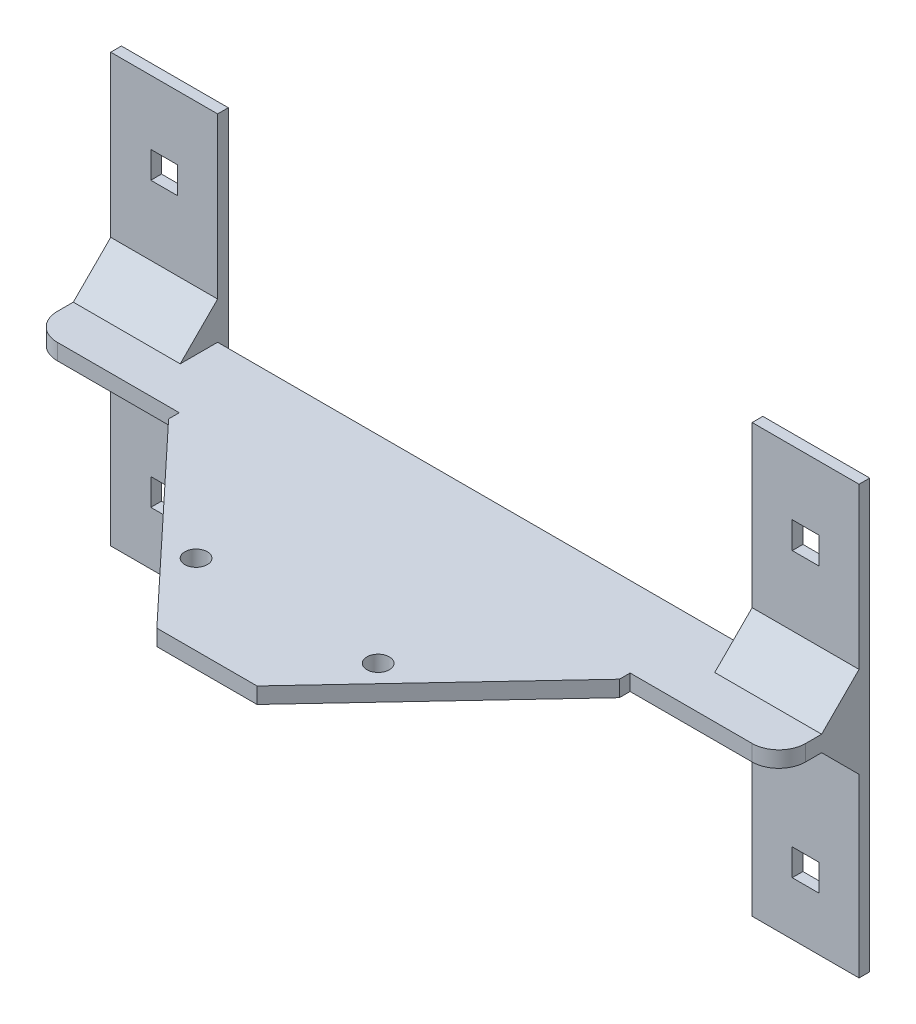
SolidWorks part; units mm, degrees
ref_plane "Front Plane" through (0, 0, 0) normal (0, 0, 1) x (1, 0, 0)
ref_plane "Top Plane" through (0, 0, 0) normal (0, 1, 0) x (1, 0, 0)
ref_plane "Right Plane" through (0, 0, 0) normal (1, 0, 0) x (0, 0, -1)
sketch "Sketch1" plane through (0, 0, 0) normal (0, 1, 0) x (1, 0, 0)
  line L0 (39.4127, 0.6403) -> (-2.757, 45.6403)
  line L2 (-2.757, 45.6403) -> (39.4127, 45.6403)
  line L3 (39.4127, 45.6403) -> (39.4127, 0.6403)
  line L4 (-2.757, 45.6403) -> (-2.757, 47.6403)
  line L5 (-2.757, 47.6403) -> (39.4127, 47.6403)
  line L6 (39.4127, 47.6403) -> (39.4127, 45.6403)
  circle A0 centre (22.3813, 25.641) radius 2.1
  dimension "D1" = 2
sketch "Sketch4" plane through (0, 0, 0) normal (0, 1, 0) x (1, 0, 0)
  line L0 (-2.757, 47.6403) -> (81.5825, 47.6403)
  line L1 (39.4127, 47.6403) -> (39.4127, 0.6403)
  line L2 (39.4127, 0.6403) -> (-2.757, 45.6403)
  line L3 (-2.757, 45.6403) -> (-2.757, 47.6403)
  line L4 (39.4127, 0.6403) -> (81.5825, 45.6403)
  line L5 (81.5825, 45.6403) -> (81.5825, 47.6403)
  circle A0 centre (22.3813, 25.641) radius 2.1
  circle A1 centre (56.4442, 25.641) radius 2.1
extrude "Boss-Extrude3" add sketch "Sketch4" along normal blind 1.2 contours L3 L2 L1 L0 A0 | L4 L5 L0 L1 A1
sketch "Sketch5" plane through (0, 0, 0) normal (0, -1, 0) x (-1, 0, 0)
  line L1 (2.757, 45.6403) -> (-81.5825, 45.6403)
  line L2 (2.757, 45.6403) -> (2.757, 47.6403)
  line L3 (2.757, 47.6403) -> (-81.5825, 47.6403)
  line L4 (-81.5825, 45.6403) -> (-81.5825, 47.6403)
extrude "Boss-Extrude4" add sketch "Sketch5" along normal blind 2.4
sketch "Sketch6" plane through (0, -2.4, 0) normal (0, -1, 0) x (-1, 0, 0)
  line L0 (2.757, 47.6403) -> (-81.5825, 47.6403)
  line L1 (-81.5825, 47.6403) -> (-81.5825, 45.6403)
  line L2 (-81.5825, 45.6403) -> (-39.4127, 0.6403)
  line L3 (-39.4127, 0.6403) -> (2.757, 45.6403)
  line L4 (2.757, 45.6403) -> (2.757, 47.6403)
  circle A0 centre (-22.3813, 25.641) radius 2.1
  circle A1 centre (-56.4442, 25.641) radius 2.1
extrude "Boss-Extrude5" add sketch "Sketch6" along normal blind 1.2
sketch "Sketch7" plane through (0, -3.6, 0) normal (0, -1, 0) x (-1, 0, 0)
  line L1 (15.2482, -5.1813) -> (-88.8196, -5.1813)
  line L2 (15.2482, -5.1813) -> (15.2482, 55.4712)
  line L3 (15.2482, 55.4712) -> (-88.8196, 55.4712)
  line L4 (-88.8196, -5.1813) -> (-88.8196, 55.4712)
extrude "Cut-Extrude1" cut sketch "Sketch7" against normal up to surface (3.6 mm away) contours L2 L1 L4 L3 up to face at (56.4442, 0, -23.541)
sketch "Sketch8" plane through (0, 1.2, 0) normal (0, 1, 0) x (1, 0, 0)
  line L0 (-2.757, 47.6403) -> (81.5825, 47.6403) construction
  line L1 (109.4127, 47.6403) -> (-30.5873, 47.6403)
  line L2 (39.4127, 47.6403) -> (39.4127, 62.6403)
  line L3 (109.4127, 62.6403) -> (-30.5873, 62.6403)
  line L4 (-30.5873, 47.6403) -> (-30.5873, 62.6403)
  line L5 (109.4127, 47.6403) -> (109.4127, 62.6403)
  line M11 (81.5825, 47.6403) -> (-2.757, 47.6403)
  dimension "D1" = 70
  dimension "D2" = 15
extrude "Boss-Extrude6" add sketch "Sketch8" against normal up to surface (1.2 mm away) contours L4 L1 L2 L3 | L1 L5 L3 L2 M11 up to face at (56.4442, 0, -23.541)
sketch "Sketch9" plane through (0, 1.2, 0) normal (0, 1, 0) x (1, 0, 0)
  line L0 (30.0417, 10.6403) -> (48.7838, 10.6403)
  line L1 (39.4127, 0.6403) -> (-2.757, 45.6403) construction
  line L2 (39.4127, 0.6403) -> (81.5825, 45.6403) construction
  line L3 (48.7838, 10.6403) -> (39.4127, 0.6403)
  line L4 (30.0417, 10.6403) -> (39.4127, 0.6403)
  dimension "D1" = 10
extrude "Cut-Extrude2" cut sketch "Sketch9" against normal blind 10
sketch "Sketch10" plane through (0, 1.2, 0) normal (0, 1, 0) x (1, 0, 0)
  line L0 (-2.757, 47.6403) -> (-2.757, 45.6403)
  line L1 (-30.5873, 62.6403) -> (109.4127, 62.6403)
  line L2 (-30.5873, 62.6403) -> (-30.5873, 47.6403)
  line L3 (-30.5873, 47.6403) -> (-2.757, 47.6403)
  line L4 (109.4127, 62.6403) -> (109.4127, 47.6403)
  line L5 (-2.757, 45.6403) -> (30.0417, 10.6403)
  line L6 (30.0417, 10.6403) -> (48.7838, 10.6403)
  line L7 (48.7838, 10.6403) -> (81.5825, 45.6403)
  line L8 (81.5825, 45.6403) -> (81.5825, 47.6403)
  line L9 (81.5825, 47.6403) -> (109.4127, 47.6403)
  circle A0 centre (22.3813, 25.641) radius 2.1
  circle A1 centre (56.4442, 25.641) radius 2.1
extrude "Boss-Extrude7" add sketch "Sketch10" along normal blind 1.8
sketch "Sketch11" plane through (0, 0, -62.6403) normal (0, 0, -1) x (-1, 0, 0)
  line L0 (-39.4127, 3) -> (-39.4127, 0) construction
  line L1 (-109.4127, 0) -> (-89.4127, 0)
  line L2 (-109.4127, -40) -> (-109.4127, 40)
  line L3 (-109.4127, 40) -> (-89.4127, 40)
  line L4 (-89.4127, -40) -> (-89.4127, 40)
  line L5 (-109.4127, 3) -> (30.5873, 3) construction
  line L6 (30.5873, 0) -> (-109.4127, 0) construction
  line L7 (-109.4127, -40) -> (-89.4127, -40)
  line L8 (30.5873, 40) -> (10.5873, 40)
  line L9 (10.5873, -40) -> (10.5873, 40)
  line L10 (30.5873, 0) -> (10.5873, 0)
  line L11 (30.5873, -40) -> (30.5873, 40)
  line L12 (10.5873, -40) -> (30.5873, -40)
  line M7 (-109.4127, 0) -> (30.5873, 0)
  line M8 (30.5873, 0) -> (30.5873, 3)
  line M9 (30.5873, 3) -> (-109.4127, 3)
  line M10 (-109.4127, 3) -> (-109.4127, 0)
  dimension "D1" = 20
  dimension "D2" = 40
extrude "Boss-Extrude8" add sketch "Sketch11" along normal blind 2 contours L4 L3 L2 M9 | L2 L7 L4 M7 | L4 M7 M9 M10 | L11 L8 L9 M9 | L9 M7 M8 M9 | L9 L12 L11 M7
sketch "Sketch12" plane through (0, 0, -64.6403) normal (0, 0, -1) x (-1, 0, 0)
  line L0 (-99.4127, 40) -> (-99.4127, -40) construction
  line L1 (-109.4127, 40) -> (-89.4127, 40) construction
  line L2 (-109.4127, -40) -> (-89.4127, -40) construction
  line L3 (-89.4127, 3) -> (10.5873, 3) construction
  line L4 (-101.9127, 23) -> (-96.9127, 23)
  line L5 (-101.9127, 23) -> (-101.9127, 28)
  line L6 (-101.9127, 28) -> (-96.9127, 28)
  line L7 (-96.9127, 23) -> (-96.9127, 28)
  line L8 (-101.9127, 23) -> (-96.9127, 28) construction
  line L9 (-101.9127, 28) -> (-96.9127, 23) construction
  line L10 (10.5873, 0) -> (-89.4127, 0) construction
  line L11 (-101.9127, -30) -> (-96.9127, -30)
  line L12 (-101.9127, -30) -> (-101.9127, -25)
  line L13 (-101.9127, -25) -> (-96.9127, -25)
  line L14 (-96.9127, -30) -> (-96.9127, -25)
  line L15 (-101.9127, -30) -> (-96.9127, -25) construction
  line L16 (-101.9127, -25) -> (-96.9127, -30) construction
  line L17 (-39.4127, 3) -> (-39.4127, 0) construction
  line L18 (23.0873, -25) -> (18.0873, -25)
  line L19 (18.0873, -30) -> (18.0873, -25)
  line L20 (23.0873, -30) -> (18.0873, -30)
  line L21 (23.0873, -30) -> (23.0873, -25)
  line L22 (23.0873, 28) -> (18.0873, 28)
  line L23 (18.0873, 23) -> (18.0873, 28)
  line L24 (23.0873, 23) -> (18.0873, 23)
  line L25 (23.0873, 23) -> (23.0873, 28)
  point P6 (-99.4127, 25.5)
  point P13 (-99.4127, -27.5)
  dimension "D1" = 5
  dimension "D2" = 5
  dimension "D3" = 20
  dimension "D4" = 5
  dimension "D5" = 5
  dimension "D6" = 25
extrude "Cut-Extrude3" cut sketch "Sketch12" against normal blind 22
chamfer "Chamfer2" distance 7 angle 45 4 edges at (-20.5873, 0, -62.6403) (-20.5873, 3, -62.6403) (99.4127, 3, -62.6403) (99.4127, 0, -62.6403)
fillet "Fillet1" radius 5 2 edges at (109.4127, 1.5, -47.6403) (-30.5873, 1.5, -47.6403)
